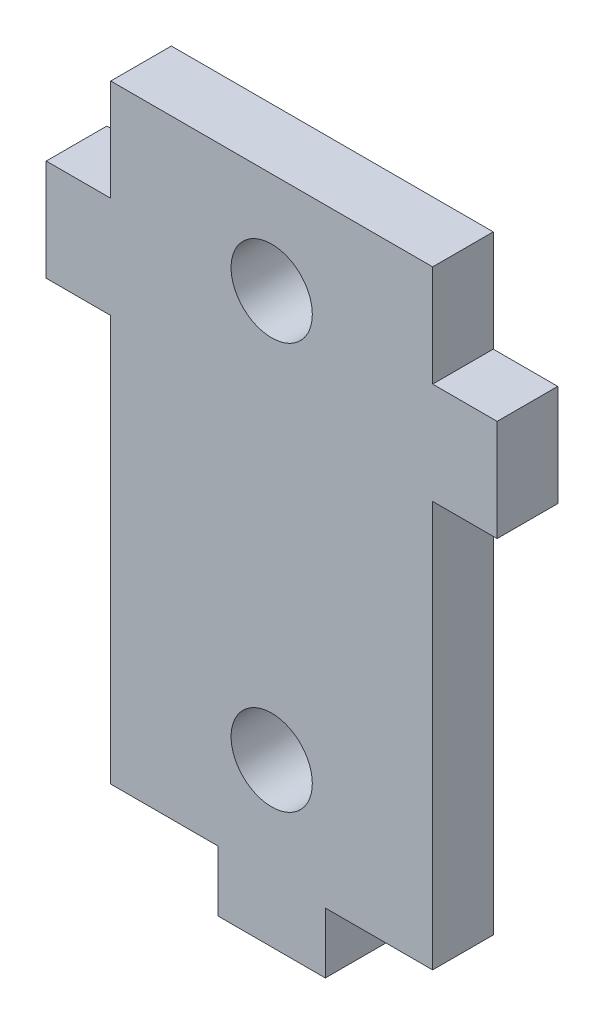
SolidWorks part; units mm, degrees
ref_plane "Front Plane" through (0, 0, 0) normal (0, 0, 1) x (1, 0, 0)
ref_plane "Top Plane" through (0, 0, 0) normal (0, 1, 0) x (1, 0, 0)
ref_plane "Right Plane" through (0, 0, 0) normal (1, 0, 0) x (0, 0, -1)
sketch "Sketch1" plane through (0, 0, 0) normal (0, 0, 1) x (1, 0, 0)
  line L0 (5.2833, 59.959) -> (5.2833, 0) construction
  line L1 (0, 0) -> (10.5667, 0) construction
  line L2 (-2.2167, 18.9845) -> (-2.2167, 59.959)
  line L3 (-2.2167, 59.959) -> (12.7833, 59.959)
  line L4 (12.7833, 18.9845) -> (12.7833, 59.959)
  line L5 (5.2833, 49.9795) -> (5.2833, 59.959) construction
  line L6 (5.2833, 9.9795) -> (5.2833, 0) construction
  line L7 (12.7833, 18.9845) -> (21.1333, 0)
  line L8 (21.1333, 0) -> (10.5667, 0)
  line L9 (-2.2167, 18.9845) -> (-10.5667, 0)
  line L10 (-10.5667, 0) -> (0, 0)
  line L11 (10.5667, 0) -> (10.5667, -5.969)
  line L12 (10.5667, -5.969) -> (0, -5.969)
  line L13 (0, -5.969) -> (0, 0)
  circle A0 centre (5.2833, 49.9795) radius 4
  circle A1 centre (5.2833, 9.9795) radius 4
  dimension "D3" = 40
  dimension "D4" = 8
  dimension "D1" = 60
  dimension "D2" = 15
  dimension "D5" = 10.5667
  dimension "D6" = 5.969
  dimension "D7" = 18.9845
extrude "Boss-Extrude1" add sketch "Sketch1" along normal blind 5.969
sketch "Sketch4" plane through (0, 0, 0) normal (0, 0, -1) x (-1, 0, 0)
  line L0 (2.2167, 59.959) -> (2.2167, 18.9845) construction
  line L1 (2.2167, 49.959) -> (16.9167, 49.959)
  line L2 (2.2167, 49.959) -> (2.2167, 39.959)
  line L3 (2.2167, 39.959) -> (16.9167, 39.959)
  line L4 (16.9167, 49.959) -> (16.9167, 39.959)
  line L5 (2.2167, 49.959) -> (16.9167, 39.959) construction
  line L6 (2.2167, 39.959) -> (16.9167, 49.959) construction
  line L7 (-12.7833, 18.9845) -> (-12.7833, 59.959) construction
  line L8 (-12.7833, 49.959) -> (-27.4833, 49.959)
  line L9 (-12.7833, 49.959) -> (-12.7833, 39.959)
  line L10 (-12.7833, 39.959) -> (-27.4833, 39.959)
  line L11 (-27.4833, 49.959) -> (-27.4833, 39.959)
  line L12 (-12.7833, 49.959) -> (-27.4833, 39.959) construction
  line L13 (-12.7833, 39.959) -> (-27.4833, 49.959) construction
  line L14 (-5.2833, -5.969) -> (-5.2833, 59.959) construction
  line L15 (0, -5.969) -> (-10.5667, -5.969) construction
  line L16 (-12.7833, 59.959) -> (2.2167, 59.959) construction
  point P4 (9.5667, 44.959)
  point P11 (-20.1333, 44.959)
  dimension "D1" = 22.2
  dimension "D2" = 10
  dimension "D3" = 10
extrude "Boss-Extrude4" add sketch "Sketch4" against normal blind 5.969
sketch "Sketch5" plane through (0, 0, 5.969) normal (0, 0, 1) x (1, 0, 0)
  line L0 (-10.5667, 0) -> (-10.5667, 59.959)
  line L1 (-10.5667, 59.959) -> (21.1333, 59.959)
  line L2 (21.1333, 59.959) -> (21.1333, 0)
  line L3 (21.1333, 0) -> (-10.5667, 0)
  line L4 (12.7833, 59.959) -> (-2.2167, 59.959) construction
  line L5 (12.7833, 18.9845) -> (12.7833, 39.959) construction
  line L6 (-2.2167, 59.959) -> (12.7833, 59.959)
  line L7 (-2.2167, 59.959) -> (-2.2167, 0)
  line L8 (-2.2167, 0) -> (12.7833, 0)
  line L9 (12.7833, 59.959) -> (12.7833, 0)
  line M6 (21.1333, 0) -> (12.7833, 18.9845)
  line M7 (12.7833, 18.9845) -> (12.7833, 39.959)
  line M8 (12.7833, 39.959) -> (27.4833, 39.959)
  line M10 (27.4833, 49.959) -> (12.7833, 49.959)
  line M11 (12.7833, 49.959) -> (12.7833, 59.959)
  line M13 (-2.2167, 59.959) -> (-2.2167, 49.959)
  line M14 (-2.2167, 49.959) -> (-16.9167, 49.959)
  line M16 (-16.9167, 39.959) -> (-2.2167, 39.959)
  line M17 (-2.2167, 39.959) -> (-2.2167, 18.9845)
  line M18 (-2.2167, 18.9845) -> (-10.5667, 0)
extrude "Boss-Extrude6" add sketch "Sketch5" against normal up to surface (5.969 mm away) contours L2 L1 M11 M10 | L2 M8 M7 M6 | L0 M18 M17 M16 | L1 L0 M14 M13 up to face at (9.2833, 49.9795, 0)
